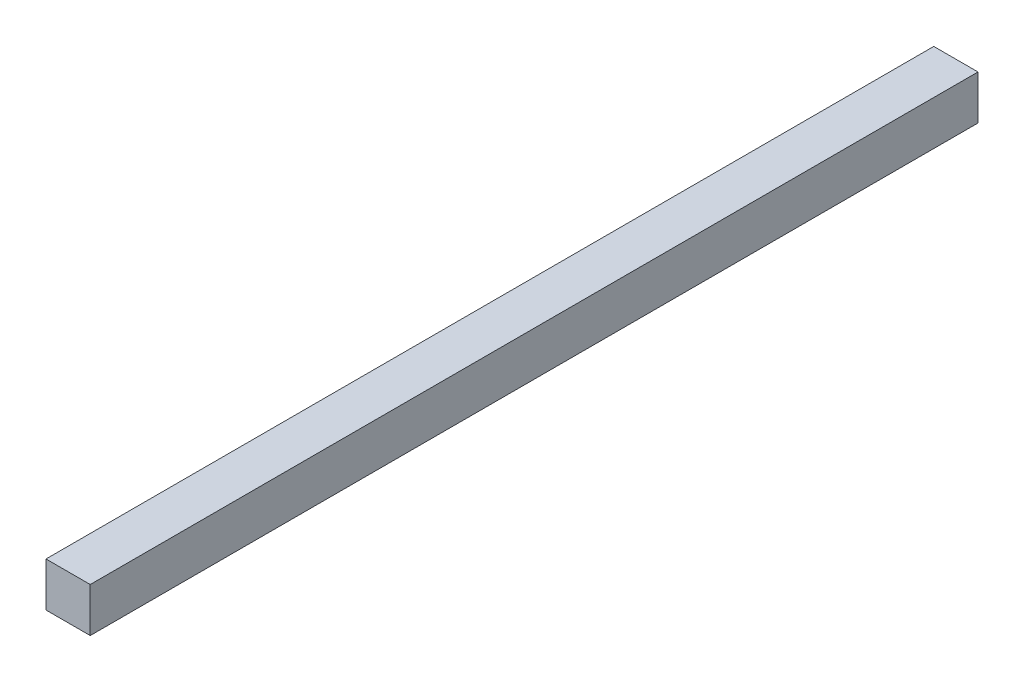
SolidWorks part; units mm, degrees
ref_plane "Front Plane" through (0, 0, 0) normal (0, 0, 1) x (1, 0, 0)
ref_plane "Top Plane" through (0, 0, 0) normal (0, 1, 0) x (1, 0, 0)
ref_plane "Right Plane" through (0, 0, 0) normal (1, 0, 0) x (0, 0, -1)
sketch "Sketch1" plane through (0, 0, 0) normal (0, 0, 1) x (1, 0, 0)
  line L1 (5, 5) -> (-5, 5)
  line L2 (5, 5) -> (5, -5)
  line L3 (5, -5) -> (-5, -5)
  line L4 (-5, 5) -> (-5, -5)
  line L5 (5, 5) -> (-5, -5) construction
  line L6 (5, -5) -> (-5, 5) construction
  point P0 (0, 0)
  dimension "D1" = 10
extrude "Boss-Extrude1" add sketch "Sketch1" along normal blind 200.7
sketch "Sketch2" plane through (0, 0, 200.7) normal (0, 0, 1) x (1, 0, 0)
  line L0 (0, 0) -> (0, 15.25) construction
  point P4 (0, 0)
  dimension "D1" = 15.25
sketch "Sketch3" plane through (0, 0, 0) normal (0, 0, -1) x (-1, 0, 0)
  line L0 (0, 0) -> (0, 15.25) construction
  line L1 (0, 0) -> (0, 15.25) construction
  point P0 (0, 0)
sketch "Sketch4" plane through (0, -5, 0) normal (0, -1, 0) x (-1, 0, 0)
  line L0 (0, -200.7) -> (0, -205.7)
  line L2 (5, -200.7) -> (-5, -200.7) construction
  line L3 (0.4276, -205) -> (1.734, -205)
  line L4 (1.734, -205) -> (1.514, -204.78)
  line L5 (1.514, -205.22) -> (1.514, -204.78) construction
  line L6 (1.514, -205.22) -> (1.734, -205)
  line L7 (2.4797, -205) -> (2.0396, -205)
  line L8 (2.2597, -205.22) -> (2.2597, -204.78)
  point P3 (0, -200.7)
  point P13 (1.514, -204.78)
  point P14 (1.514, -205)
  point P17 (2.2597, -205)
  dimension "D1" = 5
sketch "Sketch5" plane through (0, -5, 0) normal (0, -1, 0) x (-1, 0, 0)
  line L0 (0, 0) -> (0, -5)
  line L1 (5, 0) -> (-5, 0) construction
  dimension "D1" = 5
